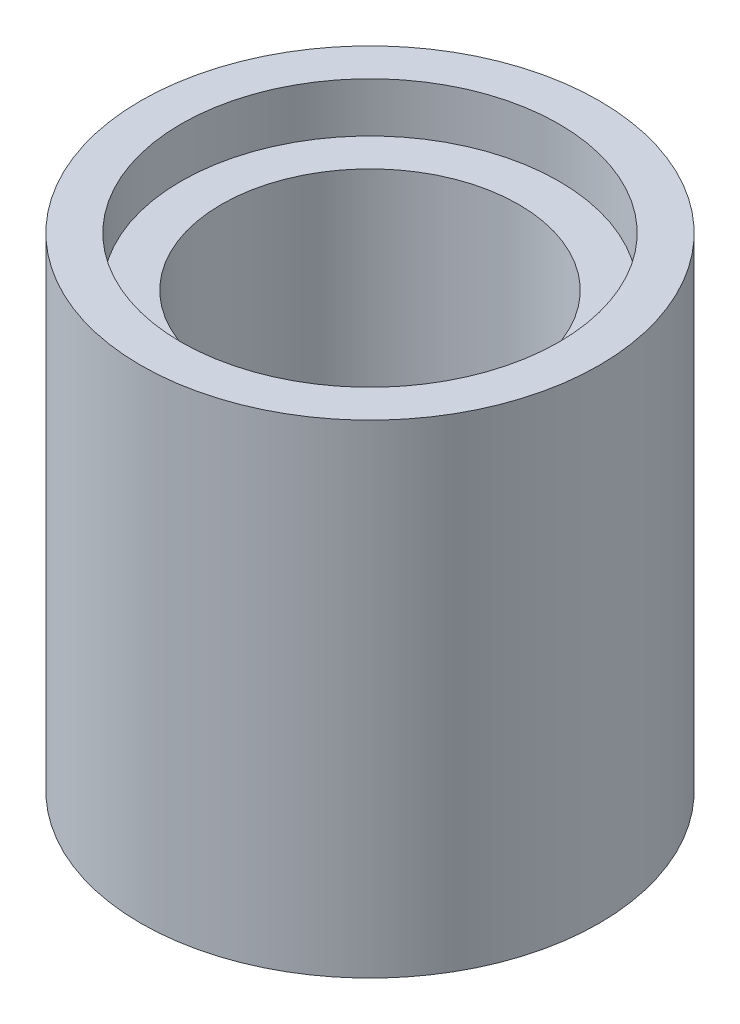
SolidWorks part; units mm, degrees
ref_plane "Front Plane" through (0, 0, 0) normal (0, 0, 1) x (1, 0, 0)
ref_plane "Top Plane" through (0, 0, 0) normal (0, 1, 0) x (1, 0, 0)
ref_plane "Right Plane" through (0, 0, 0) normal (1, 0, 0) x (0, 0, -1)
sketch "Sketch1" plane through (0, 0, 0) normal (0, 1, 0) x (1, 0, 0)
  circle A10 centre (-16, 0) radius 3.7
  point P20 (8, -3.7)
  point P25 (-8, -3.7)
  dimension "D1" = 7.4
extrude "Boss-Extrude3" add sketch "Sketch1" along normal blind 7.8 contours A10
sketch "Sketch2" plane through (0, 7.8, 0) normal (0, 1, 0) x (1, 0, 0)
  circle A6 centre (-16, 0) radius 2.4
  dimension "D1" = 4.8
extrude "Cut-Extrude6" cut sketch "Sketch2" against normal blind 7.8
sketch "Sketch3" plane through (0, 7.8, 0) normal (0, 1, 0) x (1, 0, 0)
  circle A3 centre (-16, 0) radius 3.05
  dimension "D1" = 6.1
extrude "Cut-Extrude7" cut sketch "Sketch3" against normal blind 0.8
sketch "Sketch4" plane through (0, 0, 0) normal (0, -1, 0) x (1, 0, 0)
  circle A3 centre (-16, 0) radius 3.05
  dimension "D1" = 6.1
extrude "Cut-Extrude8" cut sketch "Sketch4" against normal blind 0.8
